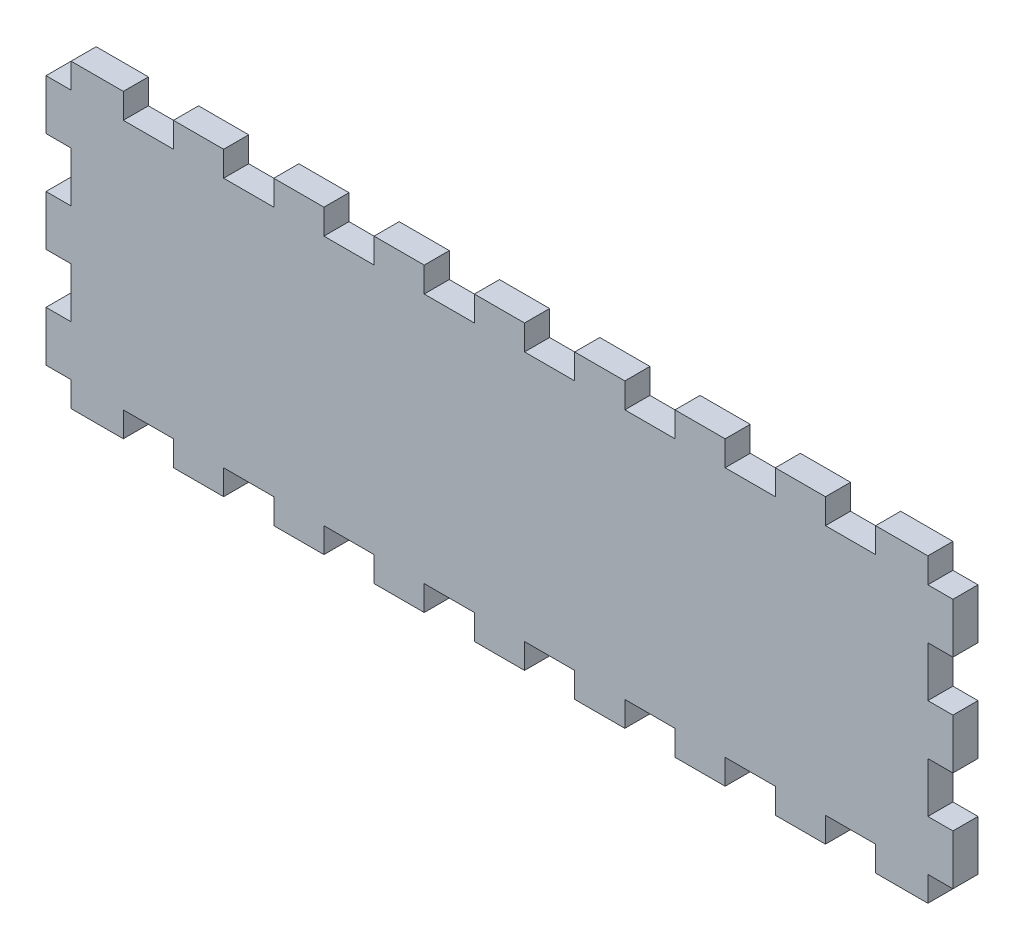
SolidWorks part; units mm, degrees
ref_plane "Front Plane" through (0, 0, 0) normal (0, 0, 1) x (1, 0, 0)
ref_plane "Top Plane" through (0, 0, 0) normal (0, 1, 0) x (1, 0, 0)
ref_plane "Right Plane" through (0, 0, 0) normal (1, 0, 0) x (0, 0, -1)
sketch "Sketch2" plane through (0, 0, 4.0363) normal (0, 0, 1) x (1, 0, 0)
  line L0 (-78, 6) -> (-78, 0)
  line L1 (-78, 0) -> (-90, 0)
  line L2 (-90, 0) -> (-90, 6)
  line L3 (-90, 6) -> (-102.5, 6)
  line L4 (-102.5, 6) -> (-102.5, 0)
  line L5 (-78, 6) -> (-66, 6)
  line L6 (-66, 6) -> (-66, 0)
  line L7 (-66, 0) -> (-54, 0)
  line L8 (-54, 0) -> (-54, 6)
  line L9 (-54, 6) -> (-42, 6)
  line L10 (-42, 6) -> (-42, 0)
  line L11 (-42, 0) -> (-30, 0)
  line L12 (-30, 0) -> (-30, 6)
  line L13 (-30, 6) -> (-18, 6)
  line L14 (-18, 6) -> (-18, 0)
  line L15 (-18, 0) -> (-6, 0)
  line L18 (-6, 0) -> (-6, 6)
  line L19 (-6, 6) -> (6, 6)
  line L20 (6, 6) -> (6, 0)
  line L21 (6, 0) -> (18, 0)
  line L22 (18, 0) -> (18, 6)
  line L23 (18, 6) -> (30, 6)
  line L24 (30, 6) -> (30, 0)
  line L25 (30, 0) -> (42, 0)
  line L27 (42, 0) -> (42, 6)
  line L29 (42, 6) -> (54, 6)
  line L30 (54, 6) -> (54, 0)
  line L31 (54, 0) -> (66, 0)
  line L33 (66, 0) -> (66, 6)
  line L34 (66, 6) -> (78, 6)
  line L35 (78, 6) -> (78, 0)
  line L36 (78, 0) -> (90, 0)
  line L38 (90, 0) -> (90, 6)
  line L40 (90, 6) -> (102.5, 6)
  line L42 (102.5, 6) -> (102.5, 0)
  line L44 (-102.5, 0) -> (-102.5, -59.9994)
  line L45 (-102.5, -29.9997) -> (102.5, -29.9997)
  line L46 (102.5, -65.9994) -> (102.5, -59.9994)
  line L47 (90, -65.9994) -> (102.5, -65.9994)
  line L48 (90, -59.9994) -> (90, -65.9994)
  line L49 (78, -59.9994) -> (90, -59.9994)
  line L50 (78, -65.9994) -> (78, -59.9994)
  line L51 (66, -65.9994) -> (78, -65.9994)
  line L52 (66, -59.9994) -> (66, -65.9994)
  line L53 (54, -59.9994) -> (66, -59.9994)
  line L54 (54, -65.9994) -> (54, -59.9994)
  line L55 (42, -65.9994) -> (54, -65.9994)
  line L56 (42, -59.9994) -> (42, -65.9994)
  line L57 (30, -59.9994) -> (42, -59.9994)
  line L58 (30, -65.9994) -> (30, -59.9994)
  line L59 (18, -65.9994) -> (30, -65.9994)
  line L60 (18, -59.9994) -> (18, -65.9994)
  line L61 (6, -59.9994) -> (18, -59.9994)
  line L62 (6, -65.9994) -> (6, -59.9994)
  line L63 (-6, -65.9994) -> (6, -65.9994)
  line L64 (-6, -59.9994) -> (-6, -65.9994)
  line L65 (-18, -59.9994) -> (-6, -59.9994)
  line L66 (-18, -65.9994) -> (-18, -59.9994)
  line L67 (-30, -65.9994) -> (-18, -65.9994)
  line L68 (-30, -59.9994) -> (-30, -65.9994)
  line L69 (-42, -59.9994) -> (-30, -59.9994)
  line L70 (-42, -65.9994) -> (-42, -59.9994)
  line L71 (-54, -65.9994) -> (-42, -65.9994)
  line L72 (-54, -59.9994) -> (-54, -65.9994)
  line L73 (-66, -59.9994) -> (-54, -59.9994)
  line L74 (-66, -65.9994) -> (-66, -59.9994)
  line L75 (-78, -65.9994) -> (-66, -65.9994)
  line L76 (-102.5, -65.9994) -> (-102.5, -59.9994)
  line L77 (-90, -65.9994) -> (-102.5, -65.9994)
  line L78 (-90, -59.9994) -> (-90, -65.9994)
  line L79 (-78, -59.9994) -> (-90, -59.9994)
  line L80 (-78, -65.9994) -> (-78, -59.9994)
  line L82 (102.5, 0) -> (102.5, -59.9994)
  point P116 (0, 0)
  point P117 (102.5, -29.9997)
  line M11 (-78, 0) -> (-66, 0)
  dimension "D1" = 59.9994
extrude "Boss-Extrude1" add sketch "Sketch2" along normal blind 6 contours L82 L42 L40 L38 L36 L35 L34 L33 L31 L30 L29 L27 L25 L24 L23 L22 L21 L20 L19 L18 L15 L14 L13 L12 L11 L10 L9 L8 L7 L1 L2 L3 L4 L44 L45 M11
sketch "Sketch3" plane through (0, 0, 10.0363) normal (0, 0, 1) x (1, 0, 0)
  line L0 (-102.5, 6) -> (-102.5, -65.9994) construction
  line L1 (-102.5, 0) -> (-108.5, 0)
  line L2 (-102.5, 0) -> (-102.5, -12)
  line L3 (-102.5, -12) -> (-108.5, -12)
  line L4 (-108.5, 0) -> (-108.5, -12)
  line L5 (-90, 6) -> (-102.5, 6) construction
  line L6 (108.5, 0) -> (108.5, -12)
  line L7 (108.5, 0) -> (102.5, 0)
  line L8 (102.5, 0) -> (102.5, -12)
  line L9 (108.5, -12) -> (102.5, -12)
  line L10 (108.5, -24) -> (108.5, -36)
  line L11 (108.5, -24) -> (102.5, -24)
  line L12 (102.5, -24) -> (102.5, -36)
  line L13 (108.5, -36) -> (102.5, -36)
  line L14 (108.5, -48) -> (108.5, -60)
  line L15 (108.5, -48) -> (102.5, -48)
  line L16 (102.5, -48) -> (102.5, -60)
  line L17 (108.5, -60) -> (102.5, -60)
  line L18 (-102.5, -24) -> (-102.5, -36)
  line L19 (-102.5, -24) -> (-108.5, -24)
  line L20 (-108.5, -24) -> (-108.5, -36)
  line L21 (-102.5, -36) -> (-108.5, -36)
  line L22 (-102.5, -48) -> (-102.5, -60)
  line L23 (-102.5, -48) -> (-108.5, -48)
  line L24 (-108.5, -48) -> (-108.5, -60)
  line L25 (-102.5, -60) -> (-108.5, -60)
  line L26 (102.5, 6) -> (102.5, -65.9994) construction
  line L34 (-102.5, 6) -> (-102.5, -65.9994) construction
  point P8 (0, 0)
  point P31 (0, 0)
  point P32 (0, 0)
  point P33 (0, 0)
  point P35 (0, 0)
  point P36 (0, 0)
  dimension "D1" = 12
  dimension "D2" = 6
  dimension "D3" = 6
  dimension "D6" = 12
  dimension "D4" = 2
  dimension "D5" = 3
extrude "Boss-Extrude2" add sketch "Sketch3" against normal blind 6
